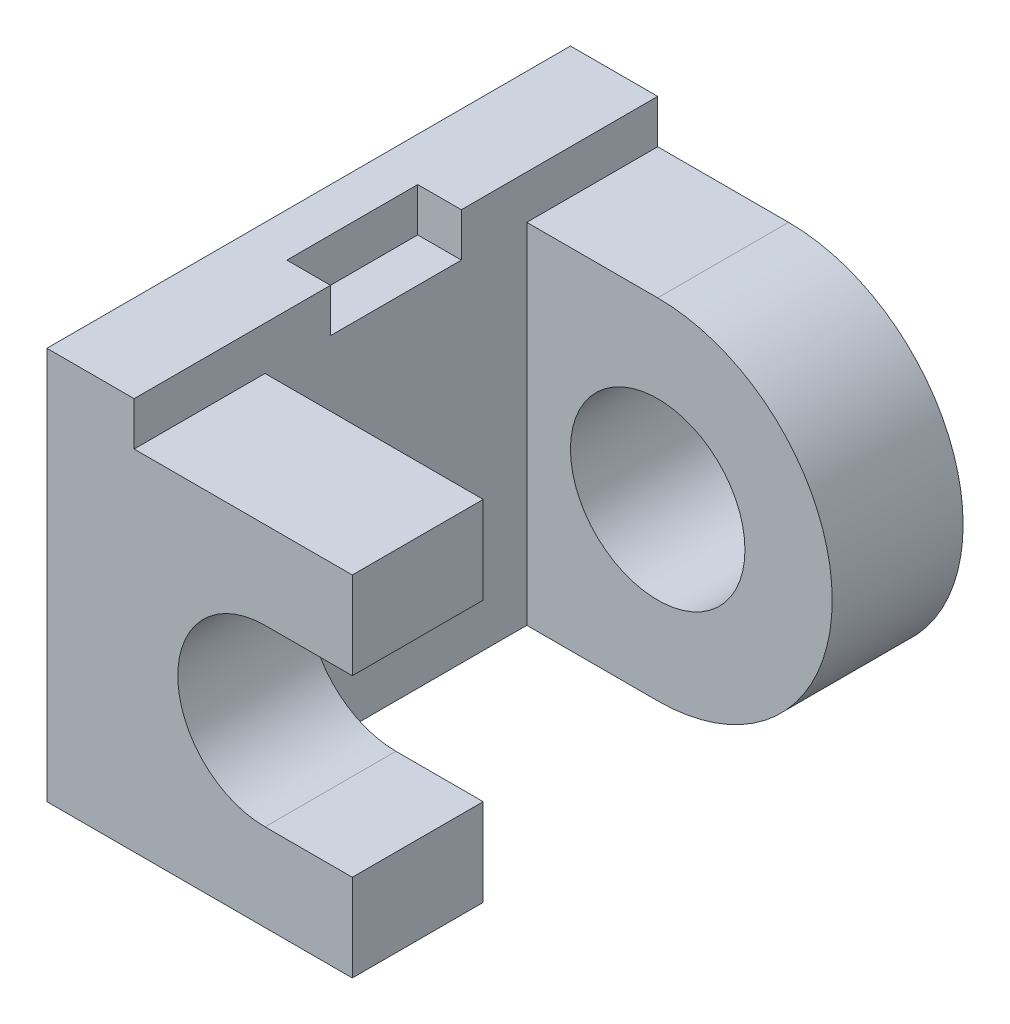
SolidWorks part; units mm, degrees
ref_plane "Front" through (0, 0, 0) normal (0, 0, 1) x (1, 0, 0)
ref_plane "Top" through (0, 0, 0) normal (0, 1, 0) x (1, 0, 0)
ref_plane "Right" through (0, 0, 0) normal (1, 0, 0) x (0, 0, -1)
sketch "Sketch2" plane through (0, 0, 0) normal (0, 1, 0) x (1, 0, 0)
  line L0 (0, 0) -> (0, 12)
  line L1 (0, 12) -> (9, 12)
  line L2 (9, 12) -> (9, 9)
  line L3 (9, 9) -> (2, 9)
  line L4 (2, 9) -> (2, 3)
  line L5 (2, 3) -> (7, 3)
  line L6 (7, 3) -> (7, 0)
  line L7 (7, 0) -> (0, 0)
  dimension "D1" = 3
  dimension "D2" = 7
  dimension "D3" = 9
  dimension "D4" = 5
  dimension "D5" = 12
  dimension "D6" = 6
extrude "Boss-Extrude1" add sketch "Sketch2" along normal blind 9
sketch "Sketch3" plane through (0, 0, 0) normal (0, 0, 1) x (1, 0, 0)
  line L0 (0, 9) -> (7, 9) construction
  line L5 (2, 9) -> (9, 9)
  line L6 (2, 9) -> (2, 8)
  line L7 (2, 8) -> (9, 8)
  line L8 (9, 9) -> (9, 8)
  line L9 (9, 9) -> (9, 0) construction
  line L10 (0, 9) -> (0, 0) construction
  line L11 (0, 0) -> (7, 0) construction
  line L12 (5, 6) -> (8.8559, 6)
  line L13 (8.8559, 6) -> (8.8559, 2)
  line L14 (8.8559, 2) -> (5, 2)
  circle A0 centre (5, 4) radius 2
  line M5 (7, 0) -> (7, 9)
  dimension "D5" = 4
  dimension "D1" = 1
  dimension "D2" = 7
  dimension "D3" = 5
  dimension "D4" = 4
extrude "Cut-Extrude4" cut sketch "Sketch3" against normal blind 8 contours L14 L13 L12 M5 | A0 | A0 L12 M5 | A0 L14 M5 | L6 L5 L8 L7
sketch "Sketch4" plane through (0, 9, 0) normal (0, 1, 0) x (1, 0, 0)
  line L0 (2, 0) -> (2, 9) construction
  line L1 (2, 4.5) -> (1, 4.5)
  line L2 (2, 4.5) -> (2, 7.5)
  line L3 (2, 7.5) -> (1, 7.5)
  line L4 (1, 4.5) -> (1, 7.5)
  line L5 (0, 0) -> (2, 0) construction
  dimension "D1" = 1
  dimension "D2" = 3
  dimension "D3" = 4.5
extrude "Cut-Extrude5" cut sketch "Sketch4" against normal blind 1
sketch "Sketch5" plane through (0, 0, -9) normal (0, 0, 1) x (1, 0, 0)
  line L0 (9, 9) -> (9, 0) construction
  line L1 (2, 9) -> (9, 9)
  line L2 (2, 9) -> (2, 8)
  line L3 (2, 8) -> (9, 8)
  line L4 (9, 9) -> (9, 8)
  line L5 (0, 0) -> (7, 0) construction
  line L6 (9, 8) -> (9, 0)
  line L7 (9, 0) -> (5, 0)
  arc A0 (5, 8) -> (5, 0) centre (5, 4) cw
  circle A1 centre (5, 4) radius 2
  line M2 (2, 0) -> (9, 0)
  line M3 (9, 0) -> (9, 9)
  line M4 (9, 9) -> (2, 9)
  line M5 (2, 9) -> (2, 0)
  dimension "D4" = 4
  dimension "D5" = 4
  dimension "D1" = 1
  dimension "D2" = 3
  dimension "D3" = 3
extrude "Cut-Extrude6" cut sketch "Sketch5" against normal blind 11 contours L3 M5 M3 M4 | A1 | L3 A0 L6 | A0 M3 M2
